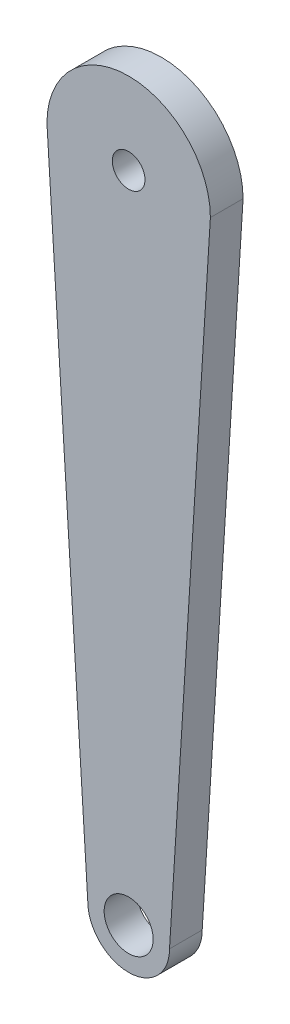
SolidWorks part; units mm, degrees
ref_plane "Front Plane" through (0, 0, 0) normal (0, 0, 1) x (1, 0, 0)
ref_plane "Top Plane" through (0, 0, 0) normal (0, 1, 0) x (1, 0, 0)
ref_plane "Right Plane" through (0, 0, 0) normal (1, 0, 0) x (0, 0, -1)
sketch "Sketch1" plane through (0, 0, 0) normal (0, 0, 1) x (1, 0, 0)
  line L2 (-25, 100) -> (-12.5, -100)
  line L4 (12.5, -100) -> (25, 100)
  arc A0 (24.8054, 96.8872) -> (-24.8054, 96.8872) centre (0, 100) ccw
  arc A1 (-12.5, -100) -> (12.5, -100) centre (0, -100) ccw
  circle A2 centre (0, 100) radius 13
  circle A3 centre (0, -100) radius 7.5
extrude "Boss-Extrude1" add sketch "Sketch1" along normal blind 10 contours L2 A1 L4 A0 A3 A2
sketch "Sketch2" plane through (0, 0, 10) normal (0, 0, 1) x (1, 0, 0)
  circle A0 centre (0, 100) radius 13
  circle A1 centre (0, 100) radius 5
extrude "Boss-Extrude2" add sketch "Sketch2" against normal up to surface (10 mm away) up to face at (7.5, -100, 0)
